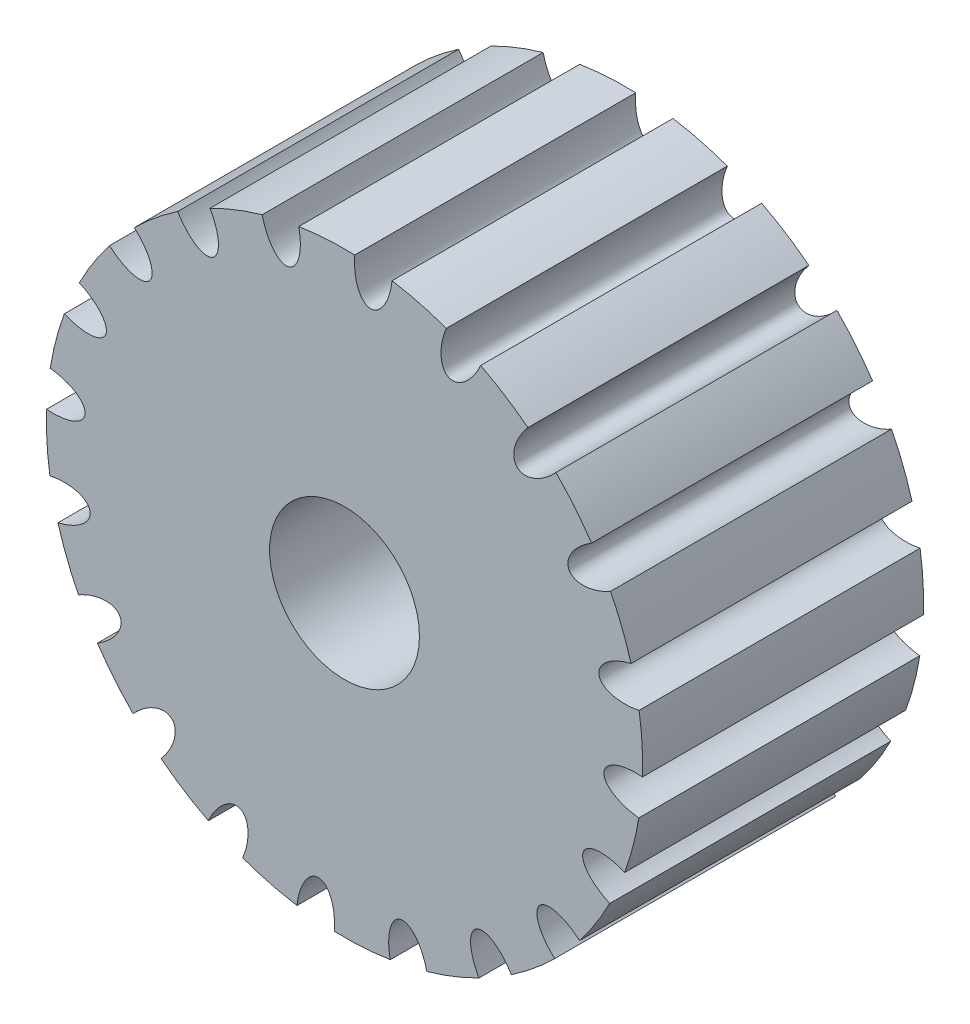
SolidWorks part; units mm, degrees
ref_plane "Спереди" through (0, 0, 0) normal (0, 0, 1) x (1, 0, 0)
ref_plane "Сверху" through (0, 0, 0) normal (0, 1, 0) x (1, 0, 0)
ref_plane "Справа" through (0, 0, 0) normal (1, 0, 0) x (0, 0, -1)
sketch "Эскиз1" plane through (0, 0, 0) normal (0, 0, 1) x (1, 0, 0)
  circle A0 centre (0, 0) radius 15.9155
  dimension "D1" = 31.831
extrude "Бобышка-Вытянуть2" add sketch "Эскиз1" along normal blind 15
sketch "Эскиз2" plane through (0, 0, 15) normal (0, 0, 1) x (1, 0, 0)
  circle A0 centre (0, 0) radius 4
  dimension "D1" = 8
extrude "Вырез-Вытянуть1" cut sketch "Эскиз2" against normal blind 15
sketch "Эскиз3" plane through (0, 0, 15) normal (0, 0, 1) x (1, 0, 0)
  circle A0 centre (0, 0) radius 15.9155 construction
  ellipse E0 centre (13.7233, 8.0607) end of major axis (15.4478, 9.0736) minor radius 1
  dimension "D1" = 4
  dimension "D2" = 2
extrude "Вырез-Вытянуть2" cut sketch "Эскиз3" against normal blind 15
pattern_circular "Круговой массив1" count 20 every 18 about axis through (0, 0, 15) along (0, 0, 1) of "Вырез-Вытянуть2"
